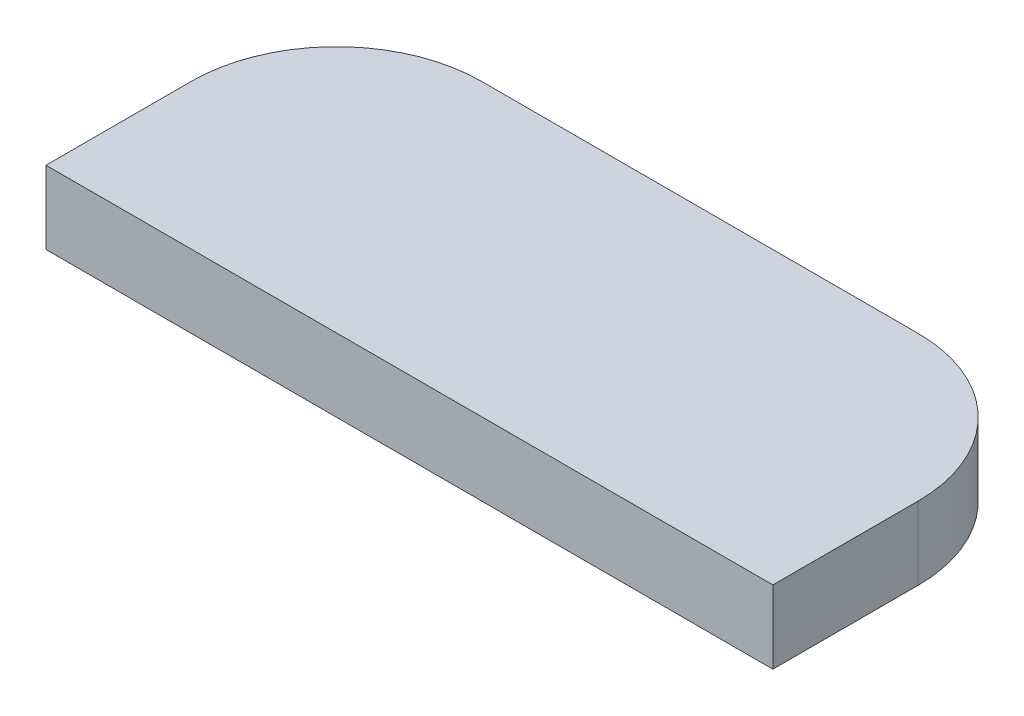
SolidWorks part; units mm, degrees
ref_plane "Front Plane" through (0, 0, 0) normal (0, 0, 1) x (1, 0, 0)
ref_plane "Top Plane" through (0, 0, 0) normal (0, 1, 0) x (1, 0, 0)
ref_plane "Right Plane" through (0, 0, 0) normal (1, 0, 0) x (0, 0, -1)
sketch "Sketch2" plane through (0, 0, 0) normal (0, 1, 0) x (1, 0, 0)
  line L0 (0, 0) -> (0, 44.45)
  line L1 (55.626, 0) -> (-55.626, 0)
  line L2 (-55.626, 0) -> (-55.626, 22.225)
  line L3 (-33.401, 44.45) -> (33.401, 44.45)
  line L4 (55.626, 0) -> (55.626, 22.225)
  arc A0 (-55.626, 22.225) -> (-33.401, 44.45) centre (-33.401, 22.225) cw
  arc A1 (55.626, 22.225) -> (33.401, 44.45) centre (33.401, 22.225) ccw
  dimension "D1" = 22.225
extrude "Boss-Extrude1" add sketch "Sketch2" along normal blind 11.176 contours A0 L3 A1 L4 L1 L2
sketch "Sketch5" plane through (0, 0, 0) normal (0, 0, 1) x (1, 0, 0)
  line L0 (22.352, 36.576) -> (22.352, 11.176)
  line L1 (55.626, 11.176) -> (-55.626, 11.176) construction
  line L2 (-22.352, 36.576) -> (-22.352, 11.176)
  line L3 (55.626, 0) -> (-55.626, 0) construction
  arc A1 (22.352, 36.576) -> (-22.352, 36.576) centre (0, 36.576) ccw
  circle A2 centre (0, 36.576) radius 7.9375
  point P10 (-22.352, 36.576)
  point P11 (-22.352, 36.576)
  dimension "D1" = 36.576
